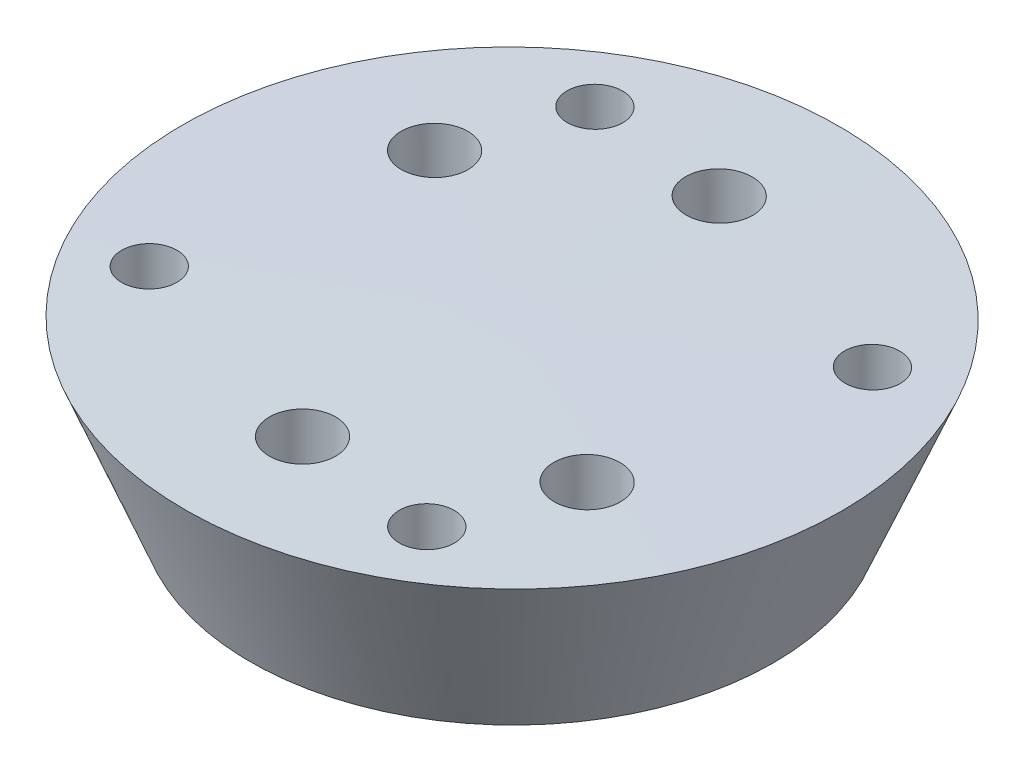
SolidWorks part; units mm, degrees
material "Lega 1060"
ref_plane "Piano frontale" through (0, 0, 0) normal (0, 0, 1) x (1, 0, 0)
ref_plane "Piano superiore" through (0, 0, 0) normal (0, 1, 0) x (1, 0, 0)
ref_plane "Piano destro" through (0, 0, 0) normal (1, 0, 0) x (0, 0, -1)
sketch "Schizzo1" plane through (0, 0, 0) normal (0, 0, 1) x (1, 0, 0)
  line L0 (0, -101.5) -> (0.1474, -81.5)
  line L1 (31.5, -101.5) -> (-31.5, -101.5) construction
  line L2 (-39.1051, -81.5) -> (39.4, -81.5) construction
  line L3 (0.1474, -81.5) -> (-39.3999, -81.5)
  line L4 (-39.3999, -81.5) -> (-31.5, -101.5)
  line L5 (-31.5, -101.5) -> (0, -101.5)
revolve "Rivoluzione1" add sketch "Schizzo1" angle 360 about L0
sketch "Schizzo2" plane through (0, -101.5, 0) normal (0, 1, 0) x (1, 0, 0)
  circle A1 centre (21.6506, -12.5) radius 2.5
  circle A2 centre (0, -25) radius 2.5
  circle A4 centre (-21.6506, 12.5) radius 2.5
  circle A5 centre (0, 25) radius 2.5
  point P15 (0, 0)
extrude "Taglio-Estrusione1" cut sketch "Schizzo2" along normal blind 21 and the other way blind 10
sketch "Schizzo3" plane through (0, -81.5, 0) normal (0, -1, 0) x (1, 0, 0)
  arc A1 (17.4043, 23.5018) -> (15.8991, 29.9761) centre (16.6517, 26.7389) ccw construction
  arc A2 (15.8991, 29.9761) -> (17.4043, 23.5018) centre (16.6517, 26.7389) ccw construction
  arc A5 (17.4043, 23.5018) -> (15.8991, 29.9761) centre (16.6517, 26.7389) ccw
  arc A6 (15.8991, 29.9761) -> (17.4043, 23.5018) centre (16.6517, 26.7389) ccw
  arc A8 (29.9761, -15.8991) -> (23.5018, -17.4043) centre (26.7389, -16.6517) ccw
  arc A9 (23.5018, -17.4043) -> (29.9761, -15.8991) centre (26.7389, -16.6517) ccw
  arc A10 (-15.8991, -29.9761) -> (-17.4043, -23.5018) centre (-16.6517, -26.7389) ccw
  arc A11 (-17.4043, -23.5018) -> (-15.8991, -29.9761) centre (-16.6517, -26.7389) ccw
  arc A12 (-29.9761, 15.8991) -> (-23.5018, 17.4043) centre (-26.7389, 16.6517) ccw
  arc A13 (-23.5018, 17.4043) -> (-29.9761, 15.8991) centre (-26.7389, 16.6517) ccw
  point P19 (0, 0)
  dimension "D1" = 4
extrude "Taglio-Estrusione2" cut sketch "Schizzo3" along normal blind 11
sketch "Schizzo4" plane through (0, 0, 0) normal (0, 1, 0) x (1, 0, 0)
  circle A0 centre (-21.6506, 12.5) radius 4
  circle A1 centre (0, 25) radius 4
  circle A3 centre (21.6506, -12.5) radius 4
  circle A4 centre (0, -25) radius 4
  circle A6 centre (21.6506, 12.5) radius 4 [skipped]
  circle A7 centre (-21.6506, -12.5) radius 4 [skipped]
  point P15 (0, 0)
  dimension "D1" = 6
extrude "Taglio-Estrusione3" cut sketch "Schizzo4" against normal blind 91
